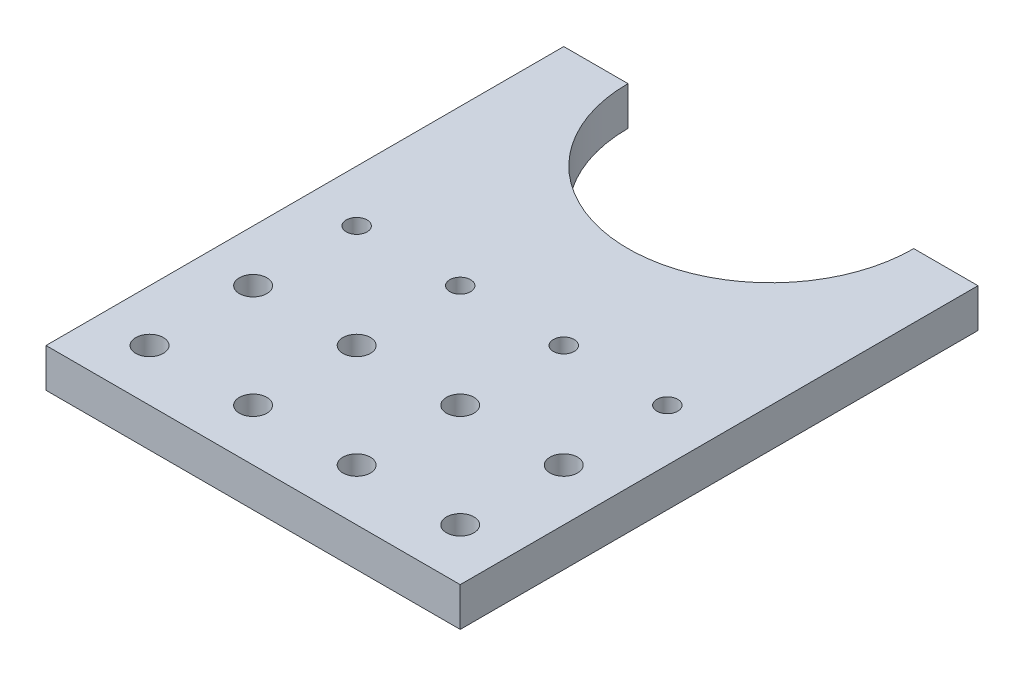
SolidWorks part; units mm, degrees
ref_plane "Front Plane" through (0, 0, 0) normal (0, 0, 1) x (1, 0, 0)
ref_plane "Top Plane" through (0, 0, 0) normal (0, 1, 0) x (1, 0, 0)
ref_plane "Right Plane" through (0, 0, 0) normal (1, 0, 0) x (0, 0, -1)
sketch "Sketch1" plane through (0, 0, 0) normal (0, 1, 0) x (1, 0, 0)
  line L1 (0, 0) -> (101.6, 0)
  line L2 (0, 0) -> (0, 127)
  line L3 (0, 127) -> (101.6, 127)
  line L4 (101.6, 0) -> (101.6, 127)
extrude "Boss-Extrude1" add sketch "Sketch1" along normal blind 9.525
sketch "Sketch2" plane through (0, 9.525, 0) normal (0, 1, 0) x (1, 0, 0)
  line L0 (101.6, 127) -> (0, 127) construction
  circle A0 centre (50.8, 127) radius 35.052
extrude "Cut-Extrude1" cut sketch "Sketch2" against normal through all
hole_wizard "1/4 Clearance Hole1" positions "Sketch4" profile "Sketch3" hole size "1/4" standard "Ansi Inch" end condition through all
sketch "Sketch4" plane through (0, 9.525, 0) normal (0, 1, 0) x (-1, 0, 0)
  point P0 (-12.7, -12.7)
sketch "Sketch3" plane through (12.7, 9.525, -12.7) normal (1, 0, 0) x (0, 0, 1)
  line L0 (0, 0) -> (0, 9.525)
  line L1 (0, 9.525) -> (3.3782, 9.525)
  line L2 (3.3782, 9.525) -> (3.3782, 0)
  line L5 (3.3782, 0) -> (0, 0)
  line L11 (0, -6.35) -> (0, 107.95) construction
  dimension "Thru Hole Dia." = 6.7564
  dimension "Thru Hole Depth" = 9.525
pattern_linear "LPattern1" count 2 spacing 25.4 along (0, 0, -1) count 4 spacing 25.4 along (1, 0, 0) of "1/4 Clearance Hole1"
hole_wizard "Tap Drill for 1/4-20 Tap1" positions "Sketch6" profile "Sketch5" hole size "1/4-20" standard "Ansi Inch" end condition through all
sketch "Sketch6" plane through (0, 9.525, 0) normal (0, 1, 0) x (-1, 0, 0)
  point P0 (-12.7, -63.5)
sketch "Sketch5" plane through (12.7, 9.525, -63.5) normal (1, 0, 0) x (0, 0, 1)
  line L0 (0, 0) -> (0, 9.525)
  line L1 (0, 9.525) -> (2.5527, 9.525)
  line L2 (2.5527, 9.525) -> (2.5527, 0)
  line L5 (2.5527, 0) -> (0, 0)
  line L11 (0, -6.35) -> (0, 107.95) construction
  dimension "Thru Hole Dia." = 5.1054
  dimension "Thru Hole Depth" = 9.525
pattern_linear "LPattern2" count 4 spacing 25.4 along (1, 0, 0) of "Tap Drill for 1/4-20 Tap1"
